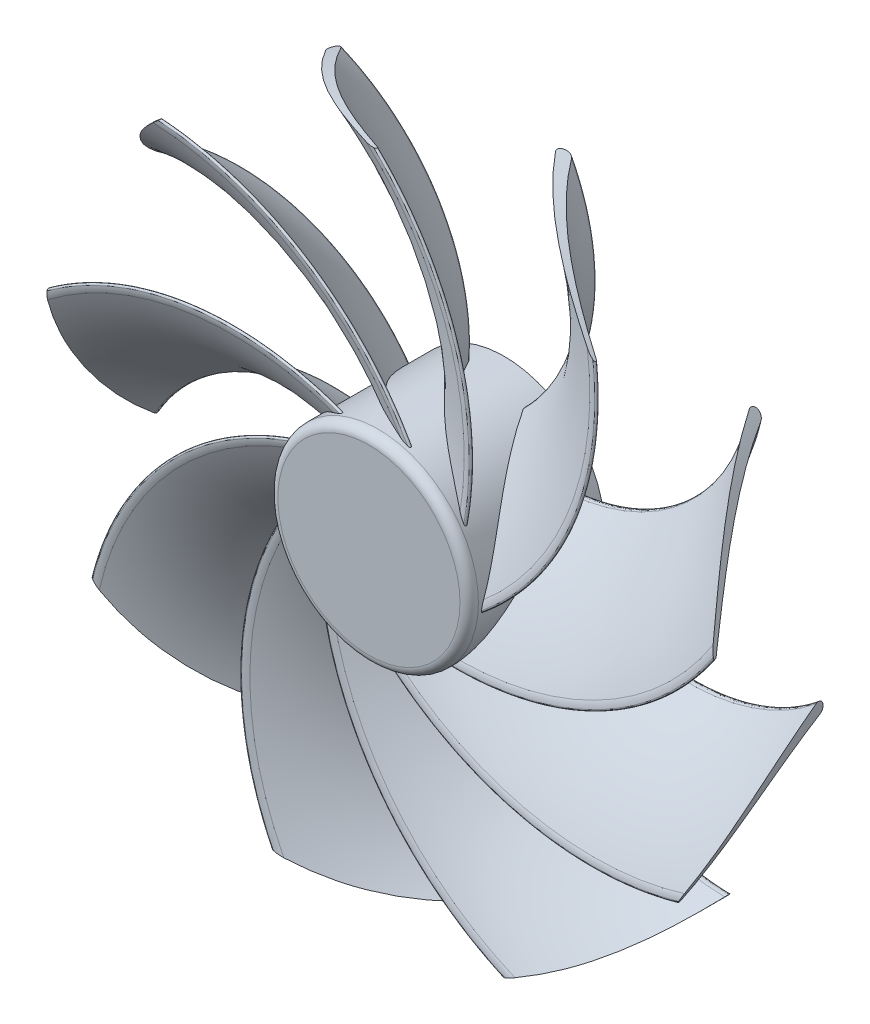
SolidWorks part; units mm, degrees
ref_plane "Front Plane" through (0, 0, 0) normal (0, 0, 1) x (1, 0, 0)
ref_plane "Top Plane" through (0, 0, 0) normal (0, 1, 0) x (1, 0, 0)
ref_plane "Right Plane" through (0, 0, 0) normal (1, 0, 0) x (0, 0, -1)
sketch "Sketch1" plane through (0, 0, 0) normal (0, 0, 1) x (1, 0, 0)
  circle A0 centre (0, 0) radius 16.3
extrude "Boss-Extrude1" add sketch "Sketch1" along normal up to vertex (22 mm away)
fillet "Fillet1" radius 1.5 1 edges at (16.3, 0, 22)
sketch "Sketch2" plane through (0, 0, 9.5) normal (0.2, -0.9798, 0) x (-0.9798, -0.2, 0)
  arc A0 (-9.8728, -10.0223) -> (6.7399, 6.0484) centre (-26.603, 23.8941) ccw
  arc A1 (6.7399, 6.0484) -> (8.1338, 5.2619) centre (7.4456, 5.6707) cw
  arc A2 (8.1338, 5.2619) -> (-8.6849, -10.1611) centre (-25.8669, 25.4577) cw
  arc A3 (-8.6849, -10.1611) -> (-9.7611, -10.4422) centre (-9.9381, -7.5632) cw
  arc A4 (-9.7611, -10.4422) -> (-9.8728, -10.0223) centre (-9.7747, -10.221) cw
sketch "Sketch4" plane through (0, 0, 9.5) normal (0, 0, 1) x (-0.9798, -0.2, 0)
  line L0 (8.1338, 0) -> (-8.6849, 0) construction
  arc A0 (8.1338, 0) -> (45.2966, -31.3357) centre (40.7486, 0.9751) ccw
sweep "Sweep1" add profiles "Sketch2" path "Sketch4"
pattern_circular "CirPattern1" count 9 over 360 about axis through (0, 0, 22) along (0, 0, 1) of "Sweep1"
sketch "Sketch5" plane through (0, 0, 22) normal (0, 0, 1) x (1, 0, 0)
  circle A0 centre (0, 0) radius 98.6344
  circle A1 centre (0, 0) radius 55.0056
extrude "Cut-Extrude2" cut sketch "Sketch5" against normal through all
